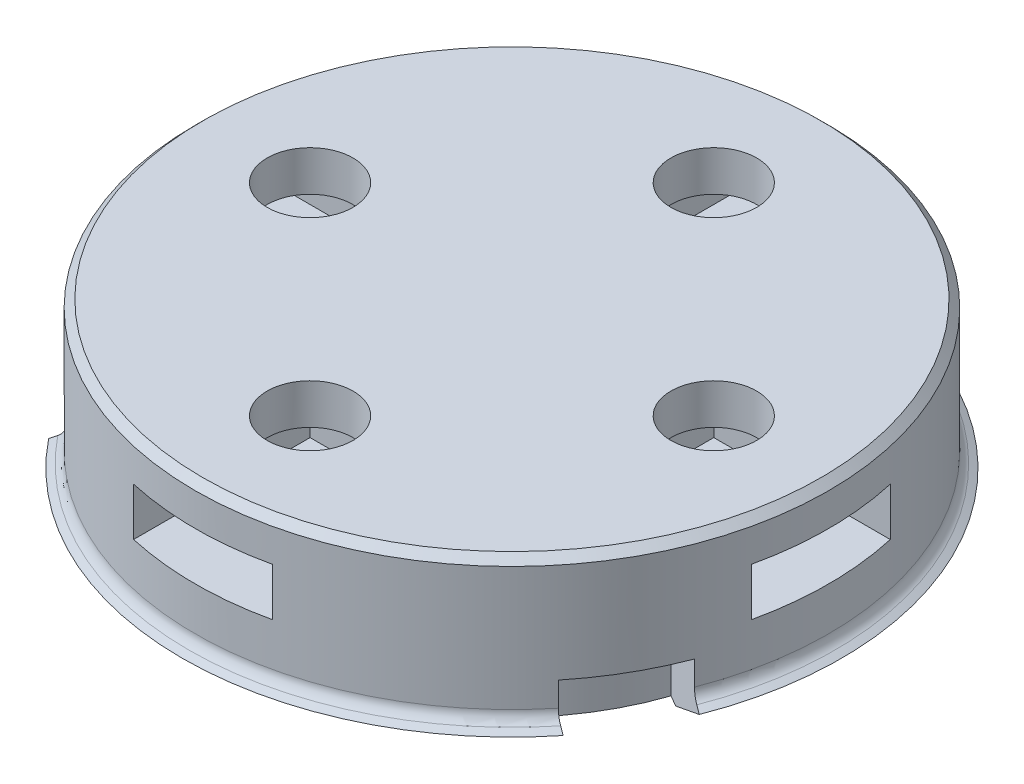
SolidWorks part; units mm, degrees
ref_plane "Front Plane" through (0, 0, 0) normal (0, 0, 1) x (1, 0, 0)
ref_plane "Top Plane" through (0, 0, 0) normal (0, 1, 0) x (1, 0, 0)
ref_plane "Right Plane" through (0, 0, 0) normal (1, 0, 0) x (0, 0, -1)
sketch "Sketch1" plane through (0, 0, 0) normal (0, 1, 0) x (1, 0, 0)
  circle A0 centre (0, 0) radius 10.05
  dimension "D1" = 20.1
extrude "Boss-Extrude1" add sketch "Sketch1" along normal blind 1.746
sketch "Sketch2" plane through (0, 1.746, 0) normal (0, 1, 0) x (1, 0, 0)
  circle A0 centre (0, 0) radius 12.55
  dimension "D1" = 25.1
extrude "Boss-Extrude2" add sketch "Sketch2" along normal blind 4
sketch "Sketch3" plane through (0, 0, 0) normal (0, -1, 0) x (1, 0, 0)
  circle A0 centre (0, 0) radius 4.5
  dimension "D1" = 9
extrude "Cut-Extrude1" cut sketch "Sketch3" against normal through all
sketch "Sketch4" plane through (0, 0, 0) normal (0, -1, 0) x (1, 0, 0)
  line L0 (0, 0) -> (0, 12.55) construction
  line L1 (0, 0) -> (0, 6.75) construction
  line L2 (0, 0) -> (5.8457, -3.375) construction
  circle A0 centre (0, 0) radius 12.55 construction
  circle A1 centre (0, 6.75) radius 2.55
  circle A2 centre (5.8457, -3.375) radius 2.55
  circle A3 centre (-5.8457, -3.375) radius 2.55
  dimension "D1" = 5.1
  dimension "D2" = 6.75
  dimension "D4" = 120
  dimension "D3" = 3
extrude "Cut-Extrude2" cut sketch "Sketch4" against normal blind 2.5
sketch "Sketch5" plane through (0, 2.5, 0) normal (0, -1, 0) x (1, 0, 0)
  circle A0 centre (0, 6.75) radius 2
  circle A1 centre (-5.8457, -3.375) radius 2
  circle A2 centre (5.8457, -3.375) radius 2
  dimension "D1" = 4
extrude "Cut-Extrude3" cut sketch "Sketch5" against normal blind 0.3
chamfer "Chamfer1" distance 0.3 angle 45 3 edges at (8.054, 0, -4.65) (-8.054, 0, -4.65) (0, 0, 9.3)
sketch "Sketch6" plane through (0, 0, 0) normal (0, -1, 0) x (1, 0, 0)
  line L0 (0, 0) -> (6.7117, 3.875) construction
  line L1 (0, 6.75) -> (5.8457, -3.375) construction
  line L2 (0, 0) -> (6.7117, 3.875) construction
  line L3 (0, 0) -> (0, -7.75) construction
  circle A0 centre (0, 0) radius 7.75 construction
  circle A1 centre (6.7117, 3.875) radius 1.1
  circle A2 centre (0, -7.75) radius 1.1
  circle A3 centre (-6.7117, 3.875) radius 1.1
  dimension "D1" = 15.5
  dimension "D2" = 2.2
  dimension "D3" = 3
  dimension "D4" = 120
extrude "Cut-Extrude4" cut sketch "Sketch6" against normal blind 2.5
ref_plane "Plane1" through (0, 1.3, 0) normal (0, -1, 0) x (-1, 0, 0)
ref_axis "Axis1" through (0, 5.746, 0) along (0, -1, 0)
sketch "Sketch10" plane through (0, 0, 0) normal (0, 0, 1) x (1, 0, 0)
  line L0 (10.05, 1.746) -> (13.5742, 1.746) construction
  line L2 (10.05, 0) -> (10.05, 1.746)
  line L3 (12.55, 1.746) -> (12.55, 5.746) construction
  line L4 (10.05, 1.746) -> (12.55, 1.746)
  line L11 (-10.05, 0) -> (10.05, 0) construction
  line L12 (10.05, 0) -> (10.55, 0) construction
  line L13 (10.55, 0) -> (13.5742, 1.746) construction
  line L14 (10.05, 0) -> (10.55, 0)
  line L15 (12.55, 1.746) -> (13.0621, 1.4504)
  line L17 (13.0621, 1.4504) -> (10.55, 0)
  dimension "D1" = 150
  dimension "D2" = 30
  dimension "D3" = 0.5
  dimension "D4" = 0.5121
revolve "Revolve1" add sketch "Sketch10" angle 360 about axis through (0, 5.746, 0) along (0, -1, 0)
sketch "Sketch7" plane through (0, 1.3, 0) normal (0, -1, 0) x (-1, 0, 0)
  line L0 (-1.975, 8.8903) -> (-1.975, 18.8903)
  line L1 (0, 10.0305) -> (-1.975, 8.8903) construction
  line L2 (-1.975, 8.8903) -> (-1.975, 6.6097)
  line L3 (-1.975, 6.6097) -> (0, 5.4695)
  line L4 (0, 5.4695) -> (1.975, 6.6097)
  line L5 (1.975, 6.6097) -> (1.975, 8.8903)
  line L6 (1.975, 8.8903) -> (0, 10.0305) construction
  line L7 (-1.975, 18.8903) -> (1.975, 18.8903)
  line L8 (1.975, 18.8903) -> (1.975, 8.8903)
  circle A0 centre (0, 7.75) radius 1.975 construction
  dimension "D1" = 3.95
  dimension "D2" = 10
extrude "Cut-Extrude5" cut sketch "Sketch7" against normal blind 1.7
sketch "Sketch11" plane through (0, 0, 0) normal (0, -1, 0) x (1, 0, 0)
  line L0 (1.975, -12.3936) -> (1.975, -6.6097) construction
  line L1 (-1.975, -19.854) -> (-1.975, -9.854)
  line L2 (1.975, -19.854) -> (1.975, -9.854)
  line L3 (-1.975, -6.6097) -> (-1.975, -12.3936) construction
  arc A0 (-1.975, -19.854) -> (1.975, -19.854) centre (0, 0) ccw
  arc A3 (-1.975, -9.854) -> (1.975, -9.854) centre (0, 0) ccw
  dimension "D1" = 10.05
  dimension "D2" = 10
extrude "Cut-Extrude6" cut sketch "Sketch11" against normal up to surface (3 mm away) up to face at (0, 3, -8.7265)
pattern_circular "CirPattern1" count 3 over 360 about axis through (0, 0, 0) along (0, 1, 0) of "Cut-Extrude5", "Cut-Extrude6"
fillet "Fillet1" radius 0.5 3 edges at (-10.8686, 1.746, -6.275) (0, 1.746, 12.55) (10.8686, 1.746, -6.275)
sketch "Sketch12" plane through (0, 5.746, 0) normal (0, 1, 0) x (1, 0, 0)
  circle A0 centre (0, 0) radius 12.55
  circle A1 centre (0, 0) radius 12.55 construction
extrude "Boss-Extrude3" add sketch "Sketch12" along normal blind 1.5
sketch "Sketch13" plane through (0, 7.246, 0) normal (0, 1, 0) x (1, 0, 0)
  circle A0 centre (0, 0) radius 8 construction
  circle A1 centre (0, -8) radius 1.7
  circle A2 centre (-8, 0) radius 1.7
  circle A3 centre (0, 8) radius 1.7
  circle A4 centre (8, 0) radius 1.7
  point P14 (0, 0)
  dimension "D1" = 16
  dimension "D2" = 3.4
  dimension "D3" = 4
extrude "Cut-Extrude7" cut sketch "Sketch13" against normal blind 3.5
sketch "Sketch14" [suppressed] plane through (0, 3.746, 0) normal (0, 1, 0) x (1, 0, 0)
  line L0 (-2.7, -9.5588) -> (-2.7, -14.5588)
  line L1 (0, -11.1177) -> (2.7, -9.5588) construction
  line L2 (2.7, -9.5588) -> (2.7, -6.4412)
  line L3 (2.7, -6.4412) -> (0, -4.8823)
  line L4 (0, -4.8823) -> (-2.7, -6.4412)
  line L5 (-2.7, -6.4412) -> (-2.7, -9.5588)
  line L6 (-2.7, -9.5588) -> (0, -11.1177) construction
  line L7 (-2.7, -14.5588) -> (2.7, -14.5588)
  line L8 (2.7, -14.5588) -> (2.7, -9.5588)
  circle A0 centre (0, -8) radius 2.7 construction
  dimension "D1" = 5.4
  dimension "D2" = 5
extrude "Cut-Extrude8" [suppressed] cut sketch "Sketch14" along normal blind 2.7
pattern_circular "CirPattern3" [suppressed] count 3 over 360 about axis through (0, 5.746, 0) along (0, -1, 0)
fillet "4 Holes Fillet" [suppressed] radius 0.5
fillet "3 Holes Fillet" [suppressed] radius 0.5
sketch "Sketch15" plane through (0, 3.746, 0) normal (0, 1, 0) x (1, 0, 0)
  line L0 (-2.75, -10.75) -> (-2.75, -15.75)
  line L1 (-2.75, -10.75) -> (2.75, -10.75) construction
  line L2 (-2.75, -10.75) -> (-2.75, -5.25)
  line L3 (-2.75, -5.25) -> (2.75, -5.25)
  line L4 (2.75, -10.75) -> (2.75, -5.25)
  line L5 (-2.75, -10.75) -> (2.75, -5.25) construction
  line L6 (-2.75, -5.25) -> (2.75, -10.75) construction
  line L7 (-2.75, -15.75) -> (2.75, -15.75)
  line L8 (2.75, -15.75) -> (2.75, -10.75)
  line L9 (-15.75, -2.75) -> (-10.75, -2.75)
  line L10 (-10.75, -2.75) -> (-5.25, -2.75)
  line L11 (-5.25, 2.75) -> (-5.25, -2.75)
  line L12 (-10.75, 2.75) -> (-5.25, 2.75)
  line L13 (-10.75, 2.75) -> (-15.75, 2.75)
  line L14 (-15.75, 2.75) -> (-15.75, -2.75)
  line L15 (-2.75, 15.75) -> (-2.75, 10.75)
  line L16 (-2.75, 10.75) -> (-2.75, 5.25)
  line L17 (2.75, 5.25) -> (-2.75, 5.25)
  line L18 (2.75, 10.75) -> (2.75, 5.25)
  line L19 (2.75, 10.75) -> (2.75, 15.75)
  line L20 (2.75, 15.75) -> (-2.75, 15.75)
  line L21 (15.75, 2.75) -> (10.75, 2.75)
  line L22 (10.75, 2.75) -> (5.25, 2.75)
  line L23 (5.25, -2.75) -> (5.25, 2.75)
  line L24 (10.75, -2.75) -> (5.25, -2.75)
  line L25 (10.75, -2.75) -> (15.75, -2.75)
  line L26 (15.75, -2.75) -> (15.75, 2.75)
  point P0 (0, -8)
  point P22 (0, 0)
  dimension "D1" = 5
  dimension "D2" = 5.5
  dimension "D3" = 4
extrude "Cut-Extrude9" cut sketch "Sketch15" along normal blind 1.9
chamfer "Chamfer2" distance 0.3 angle 45 1 edges at (0, 7.246, 12.55)
fillet "Fillet2" [suppressed] radius 0.5
fillet "Fillet3" [suppressed] radius 0.5
sketch "Sketch16" plane through (0, 0, 0) normal (0, -1, 0) x (1, 0, 0)
  circle A0 centre (0, 6.75) radius 5.25
  circle A1 centre (-5.8457, -3.375) radius 5.25
  circle A2 centre (5.8457, -3.375) radius 5.25
  dimension "D1" = 10.5
extrude "Cut-Extrude10" cut sketch "Sketch16" against normal blind 0.5
sketch "Sketch17" plane through (0, 0.5, 0) normal (0, -1, 0) x (1, 0, 0)
  line L0 (-3.496, 2.8333) -> (-2.4877, 7.3103)
  line L1 (0, 0) -> (0, 6.75) construction
  line L2 (3.496, 2.8333) -> (2.4877, 7.3103)
  line L3 (-3.496, 2.8333) -> (3.496, 2.8333)
  line L4 (4.2018, 1.611) -> (0.7057, -4.4443)
  line L5 (0.7057, -4.4443) -> (5.0871, -5.8095)
  line L6 (4.2018, 1.611) -> (7.5747, -1.5008)
  line L7 (-0.7057, -4.4443) -> (-4.2018, 1.611)
  line L8 (-4.2018, 1.611) -> (-7.5747, -1.5008)
  line L9 (-0.7057, -4.4443) -> (-5.0871, -5.8095)
  circle A0 centre (0, 6.75) radius 2.55 construction
  circle A1 centre (0, 6.75) radius 2.55 construction
  arc A2 (-2.4877, 7.3103) -> (2.4877, 7.3103) centre (0, 6.75) cw
  arc A3 (7.5747, -1.5008) -> (5.0871, -5.8095) centre (5.8457, -3.375) cw
  arc A4 (-5.0871, -5.8095) -> (-7.5747, -1.5008) centre (-5.8457, -3.375) cw
  point P26 (0, 0)
  dimension "D1" = 3
sketch "Sketch18" plane through (0, 1.3, 0) normal (0, 1, 0) x (1, 0, 0)
  circle A100 centre (6.7117, -3.875) radius 1.2
  circle A101 centre (0, 7.75) radius 1.2
  circle A102 centre (0, 7.75) radius 1.2
  circle A103 centre (-6.7117, -3.875) radius 1.2
  point P0 (0, 0)
  point P6 (0, 0)
  dimension "D1" = 0.1
  dimension "D2" = 3
extrude "Boss-Extrude4" add sketch "Sketch18" against normal blind 0.1
